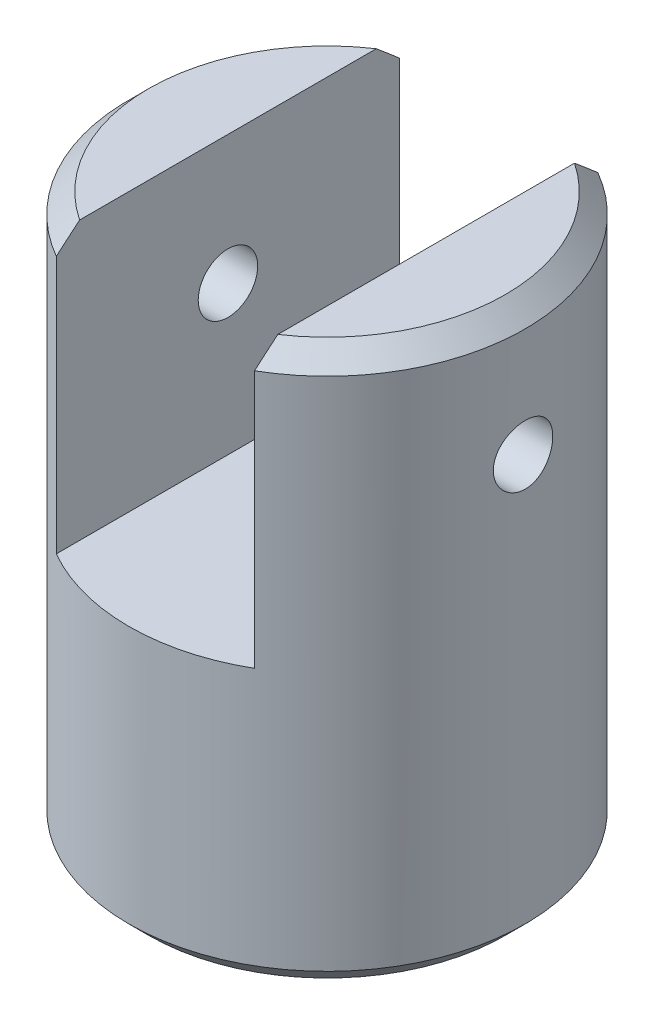
SolidWorks part; units mm, degrees
material "6061 Alloy"
ref_plane "Front Plane" through (0, 0, 0) normal (0, 0, 1) x (1, 0, 0)
ref_plane "Top Plane" through (0, 0, 0) normal (0, 1, 0) x (1, 0, 0)
ref_plane "Right Plane" through (0, 0, 0) normal (1, 0, 0) x (0, 0, -1)
sketch "Sketch1" plane through (0, 0, 0) normal (0, 1, 0) x (1, 0, 0)
  circle A0 centre (0, 0) radius 5
  dimension "D1" = 10
extrude "Boss-Extrude1" add sketch "Sketch1" along normal blind 14
chamfer "Chamfer1" distance 0.5 angle 45 2 edges at (0, 0, 5) (0, 14, 5)
sketch "Sketch2" plane through (0, 0, 0) normal (0, -1, 0) x (1, 0, 0)
  circle A0 centre (0, 0) radius 0.75
  dimension "D1" = 1.5
extrude "Cut-Extrude1" cut sketch "Sketch2" against normal up to next
sketch "Sketch3" plane through (0, 14, 0) normal (0, 1, 0) x (1, 0, 0)
  line L0 (-2.5, 5) -> (-2.5, -5)
  line L1 (2.5, 5) -> (2.5, -5)
  line L2 (2.5, -5) -> (-2.5, -5)
  line L3 (-2.5, 5) -> (2.5, 5)
  line L4 (0, 0) -> (2.5, 0) construction
  line L5 (-2.5, 0) -> (2.5, 0) construction
  circle A1 centre (0, 0) radius 5 construction
  dimension "D1" = 2.5
extrude "Cut-Extrude2" cut sketch "Sketch3" against normal blind 7
sketch "Sketch4" plane through (0, 0, 0) normal (1, 0, 0) x (0, 0, -1)
  line L0 (0, 10.75) -> (0, 0) construction
  line L1 (3.7417, 14) -> (-3.7417, 14) construction
  circle A0 centre (0, 10.75) radius 0.75
  point P2 (0, 14)
  dimension "D1" = 1.5
  dimension "D2" = 3.25
extrude "Cut-Extrude3" cut sketch "Sketch4" against normal up to next and the other way up to next
